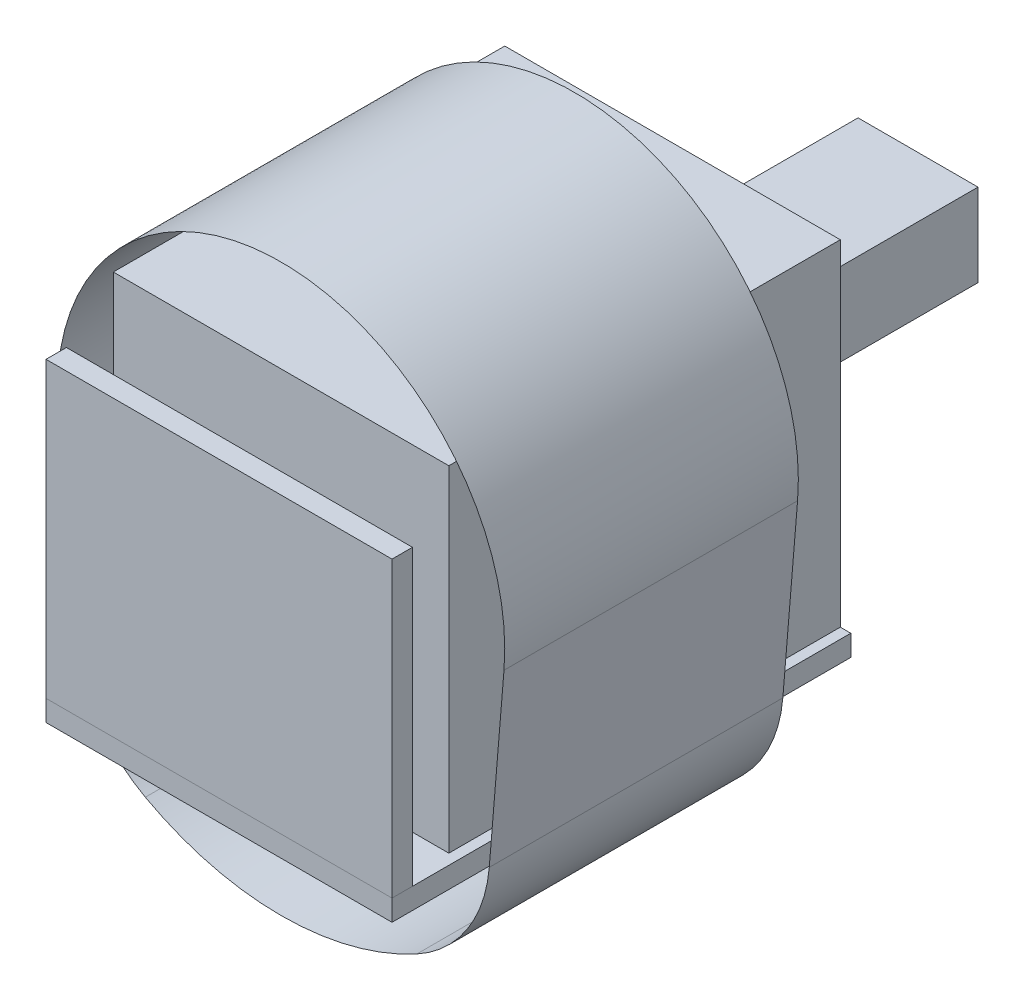
SolidWorks part; units mm, degrees
ref_plane "Front Plane" through (0, 0, 0) normal (0, 0, 1) x (1, 0, 0)
ref_plane "Top Plane" through (0, 0, 0) normal (0, 1, 0) x (1, 0, 0)
ref_plane "Right Plane" through (0, 0, 0) normal (1, 0, 0) x (0, 0, -1)
sketch "Sketch1" plane through (0, 0, 0) normal (1, 0, 0) x (0, 0, -1)
  line L1 (10.0873, 15.1707) -> (24.0873, 15.1707)
  line L2 (10.0873, 15.1707) -> (10.0873, 27.1707)
  line L3 (10.0873, 27.1707) -> (24.0873, 27.1707)
  line L4 (24.0873, 15.1707) -> (24.0873, 27.1707)
  dimension "D1" = 14
  dimension "D2" = 12
extrude "battery" add sketch "Sketch1" along normal blind 12
ref_plane "Plane1" through (0, 0, -26.0073) normal (0, 0, -1) x (-1, 0, 0)
sketch "Sketch2" plane through (0, 0, -26.0073) normal (0, 0, -1) x (-1, 0, 0)
  line L1 (-3.855, 19.5235) -> (-8.145, 19.5235)
  line L2 (-3.855, 19.5235) -> (-3.855, 22.4835)
  line L3 (-3.855, 22.4835) -> (-8.145, 22.4835)
  line L4 (-8.145, 19.5235) -> (-8.145, 22.4835)
  line L5 (-6, 22.4835) -> (-6, 26.0105) construction
  line L6 (-12, 27.1707) -> (0, 27.1707) construction
  point P12 (-6, 27.1707)
  dimension "D1" = 4.29
  dimension "D2" = 2.96
extrude "driver" add sketch "Sketch2" along normal blind 6.86 separate body
sketch "Sketch10" plane through (0, 15.1707, 0) normal (0, -1, 0) x (1, 0, 0)
  line L1 (0, -7.6801) -> (12.375, -7.6801)
  line L2 (0, -7.6801) -> (0, -24.0873)
  line L3 (0, -24.0873) -> (12.375, -24.0873)
  line L4 (12.375, -7.6801) -> (12.375, -24.0873)
extrude "PCB " add sketch "Sketch10" along normal blind 0.75 separate body
sketch "Sketch11" plane through (0, 14.4207, 0) normal (0, -1, 0) x (1, 0, 0)
  line L1 (1.1347, -23.9234) -> (10.0347, -23.9234)
  line L2 (1.1347, -23.9234) -> (1.1347, -11.2234)
  line L3 (1.1347, -11.2234) -> (10.0347, -11.2234)
  line L4 (10.0347, -23.9234) -> (10.0347, -11.2234)
  dimension "D1" = 12.7
  dimension "D2" = 8.9
extrude "KLR device" add sketch "Sketch11" along normal blind 2 separate body
sketch "Sketch9" plane through (0, 0, -10.0873) normal (0, 0, 1) x (1, 0, 0)
  line L0 (6, 22.4835) -> (6, 28.9916) construction
  line L1 (3.855, 22.4835) -> (8.145, 22.4835) construction
  line L2 (6, 22.4835) -> (6, 13.9391) construction
  line L4 (-1.4452, 15.4535) -> (-1.9727, 21.8232)
  line L5 (13.4452, 15.4535) -> (13.9727, 21.8232)
  arc A0 (13.9727, 21.8232) -> (-1.9727, 21.8232) centre (6, 22.4835) ccw
  arc A1 (13.4452, 15.4535) -> (10.8556, 11.4762) centre (8.4622, 15.8661) cw
  arc A2 (1.1444, 11.4762) -> (10.8556, 11.4762) centre (6, 20.3823) ccw
  arc A3 (-1.4452, 15.4535) -> (1.1444, 11.4762) centre (3.5378, 15.8661) ccw
  point P7 (13.2673, 13.3054)
  point P15 (-1.2673, 13.3054)
  dimension "D1" = 16
  dimension "D2" = 5
sketch "Sketch12" plane through (0, 14.4207, 0) normal (0, -1, 0) x (1, 0, 0)
  line L1 (3.044, -8.8641) -> (6.044, -8.8641)
  line L2 (3.044, -8.8641) -> (3.044, -10.3641)
  line L3 (3.044, -10.3641) -> (6.044, -10.3641)
  line L4 (6.044, -8.8641) -> (6.044, -10.3641)
  dimension "D1" = 1.5
  dimension "D2" = 3
extrude "antenna" add sketch "Sketch12" along normal blind 0.5 separate body
surface "Surface-Extrude2" sketch "Sketch9" parameters "D1"=10.5
sketch "Sketch13" plane through (0, 15.1707, 0) normal (0, 1, 0) x (1, 0, 0)
  line L0 (12.375, 24.0873) -> (12.375, 7.6801) construction
  line L1 (0, 7.6801) -> (12.375, 7.6801)
  line L2 (0, 7.6801) -> (0, 8.4108)
  line L3 (0, 8.4108) -> (12.375, 8.4108)
  line L4 (12.375, 7.6801) -> (12.375, 8.4108)
extrude "substrate" add sketch "Sketch13" along normal blind 10.5 separate body
